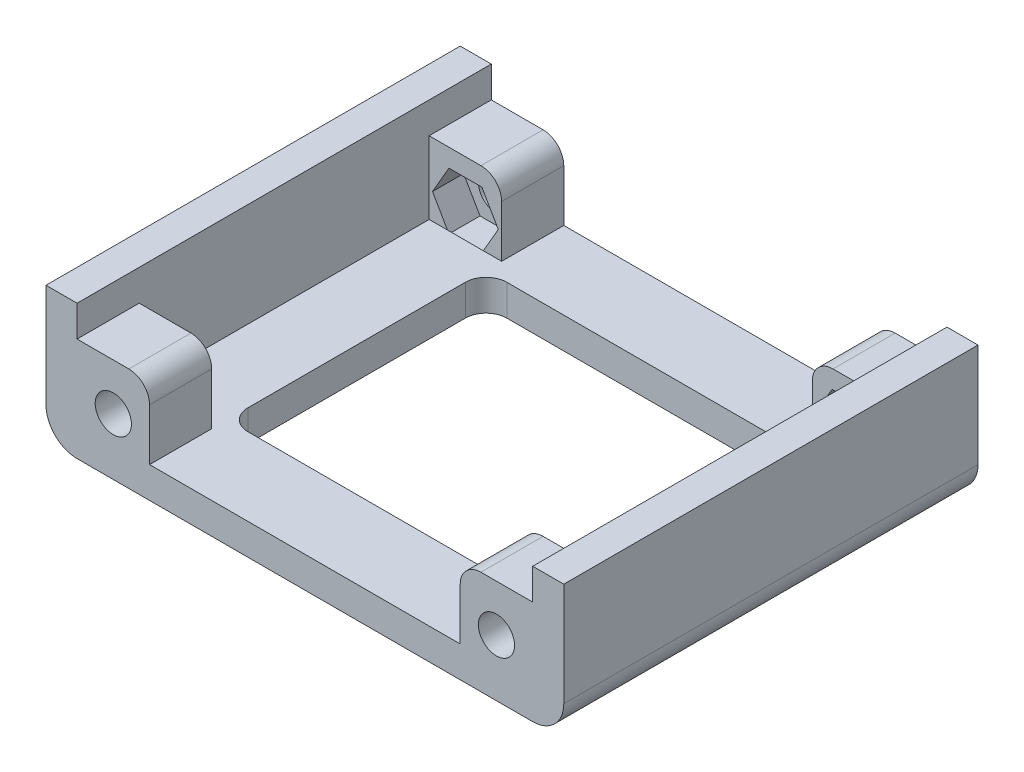
SolidWorks part; units mm, degrees
ref_plane "Front Plane" through (0, 0, 0) normal (0, 0, 1) x (1, 0, 0)
ref_plane "Top Plane" through (0, 0, 0) normal (0, 1, 0) x (1, 0, 0)
ref_plane "Right Plane" through (0, 0, 0) normal (1, 0, 0) x (0, 0, -1)
sketch "Sketch1" plane through (0, 0, 0) normal (0, 1, 0) x (1, 0, 0)
  line L1 (-25, 20) -> (25, 20)
  line L2 (-25, 20) -> (-25, -20)
  line L3 (-25, -20) -> (25, -20)
  line L4 (25, 20) -> (25, -20)
  line L5 (-25, 20) -> (25, -20) construction
  line L6 (-25, -20) -> (25, 20) construction
  point P0 (0, 0)
  dimension "D1" = 50
  dimension "D2" = 40
extrude "Boss-Extrude1" add sketch "Sketch1" along normal blind 3
sketch "Sketch2" plane through (0, 3, 0) normal (0, 1, 0) x (1, 0, 0)
  line L1 (15, -12.5) -> (-15, -12.5)
  line L2 (15, -12.5) -> (15, 12.5)
  line L3 (15, 12.5) -> (-15, 12.5)
  line L4 (-15, -12.5) -> (-15, 12.5)
  line L5 (15, -12.5) -> (-15, 12.5) construction
  line L6 (15, 12.5) -> (-15, -12.5) construction
  point P0 (0, 12.5)
  point P2 (0, 0)
  point P6 (0, 0)
  point P7 (0, 0)
  point P10 (0, 0)
  dimension "D1" = 25
  dimension "D2" = 30
extrude "Cut-Extrude1" cut sketch "Sketch2" against normal through all
sketch "Sketch3" plane through (0, 3, 0) normal (0, 1, 0) x (1, 0, 0)
  line L0 (-25, -20) -> (25, -20) construction
  line L1 (-25, 20) -> (-22, 20)
  line L2 (-25, 20) -> (-25, -20)
  line L3 (-25, -20) -> (-22, -20)
  line L4 (-22, 20) -> (-22, -20)
  line L6 (22, -20) -> (25, -20)
  line L7 (22, -20) -> (22, 20)
  line L8 (22, 20) -> (25, 20)
  line L9 (25, -20) -> (25, 20)
  dimension "D1" = 3
extrude "Boss-Extrude2" add sketch "Sketch3" along normal blind 10
sketch "Sketch4" plane through (0, 0, 20) normal (0, 0, 1) x (1, 0, 0)
  line L1 (-22, 3) -> (-15, 3)
  line L2 (-22, 3) -> (-22, 10)
  line L3 (-22, 10) -> (-15, 10)
  line L4 (-15, 3) -> (-15, 10)
  line L5 (22, 3) -> (15, 3)
  line L6 (22, 3) -> (22, 10)
  line L7 (22, 10) -> (15, 10)
  line L8 (15, 3) -> (15, 10)
  dimension "D2" = 7
  dimension "6" = 7
extrude "Boss-Extrude3" add sketch "Sketch4" against normal blind 6
sketch "Sketch5" plane through (0, 0, 20) normal (0, 0, 1) x (1, 0, 0)
  line L0 (-18.5, 10) -> (-18.5, 5.5) construction
  line L1 (-15, 10) -> (-22, 10) construction
  line L2 (18.5, 10) -> (18.5, 5.5) construction
  line L3 (-25, 0) -> (25, 0) construction
  line L4 (-18.5, 5.5) -> (18.5, 5.5) construction
  line L5 (-22, 13) -> (-22, 10) construction
  line L6 (-22, 10) -> (-15, 10) construction
  line L8 (15, 10) -> (22, 10) construction
  line L9 (15, 10) -> (15, 3) construction
  line L11 (22, 10) -> (15, 10) construction
  circle A0 centre (-18.5, 5.5) radius 1.75
  circle A1 centre (18.5, 5.5) radius 1.75
  dimension "D1" = 3.5
  dimension "D2" = 3.5
  dimension "D3" = 5.5
extrude "Cut-Extrude2" cut sketch "Sketch5" against normal through all
mirror "Mirror1" about plane through (0, 0, 0) normal (0, 0, 1) of "Cut-Extrude2", "Boss-Extrude3"
sketch "Sketch6" plane through (0, 0, -14) normal (0, 0, 1) x (1, 0, 0)
  line L7 (-15.3246, 5.5) -> (-16.9123, 8.25)
  line L8 (-16.9123, 8.25) -> (-20.0877, 8.25)
  line L9 (-20.0877, 8.25) -> (-21.6754, 5.5)
  line L10 (-21.6754, 5.5) -> (-20.0877, 2.75)
  line L11 (-20.0877, 2.75) -> (-16.9123, 2.75)
  line L12 (-16.9123, 2.75) -> (-15.3246, 5.5)
  circle A0 centre (-18.5, 5.5) radius 2.75 construction
  dimension "D1" = 5.5
extrude "Cut-Extrude3" cut sketch "Sketch6" against normal blind 3
mirror "Mirror2" about plane through (0, 0, 0) normal (1, 0, 0) of "Cut-Extrude3"
mirror "Mirror3" about plane through (0, 0, 0) normal (0, 0, 1) of "Mirror2", "Cut-Extrude3"
fillet "Fillet1" radius 3 2 edges at (-25, 0, 0) (25, 0, 0)
fillet "Fillet2" radius 2 4 edges at (15, 10, 17) (15, 10, -17) (-15, 10, -17) (-15, 10, 17)
fillet "Fillet3" radius 2 4 edges at (15, 1.5, -12.5) (-15, 1.5, -12.5) (-15, 1.5, 12.5) (15, 1.5, 12.5)
